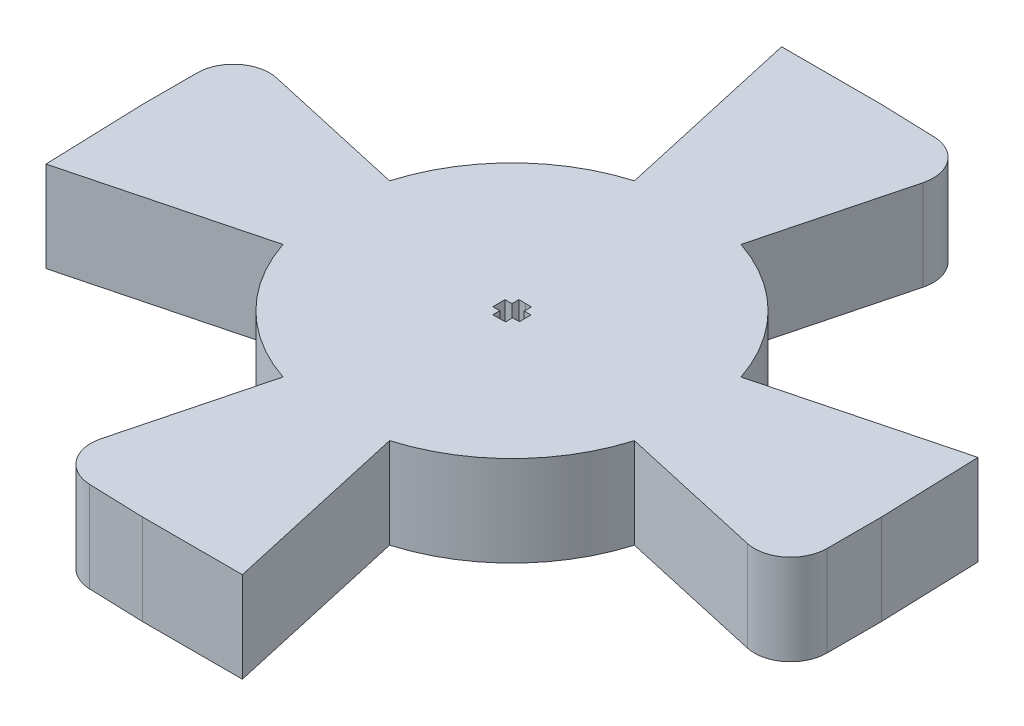
SolidWorks part; units mm, degrees
ref_plane "Front Plane" through (0, 0, 0) normal (0, 0, 1) x (1, 0, 0)
ref_plane "Top Plane" through (0, 0, 0) normal (0, 1, 0) x (1, 0, 0)
ref_plane "Right Plane" through (0, 0, 0) normal (1, 0, 0) x (0, 0, -1)
sketch "Sketch1" plane through (0, 0, 0) normal (0, 1, 0) x (1, 0, 0)
  line L0 (0.9504, 56.4023) -> (-0.9504, -56.4023) construction
  line L1 (-102.886, 0) -> (102.886, 0) construction
  line L2 (2.8313, -9.5908) -> (5.1777, -20.0637)
  line L3 (5.1777, -20.0637) -> (-0.3381, -20.0637)
  line L4 (-24.7302, 24.7302) -> (24.7302, -24.7302) construction
  line L5 (-31.3406, -31.3406) -> (31.3406, 31.3406) construction
  line L6 (-5.8507, -19.8779) -> (-0.3381, -20.0637)
  line L7 (-3.1528, -9.49) -> (-5.8507, -19.8779)
  line L8 (9.5908, -2.8313) -> (20.0637, -5.1777)
  line L9 (20.0637, -5.1777) -> (20.0637, 0.3381)
  line L10 (19.8779, 5.8507) -> (20.0637, 0.3381)
  line L11 (9.49, 3.1528) -> (19.8779, 5.8507)
  line L12 (-9.49, -3.1528) -> (-19.8779, -5.8507)
  line L13 (-19.8779, -5.8507) -> (-20.0637, -0.3381)
  line L14 (-20.0637, 5.1777) -> (-20.0637, -0.3381)
  line L15 (-9.5908, 2.8313) -> (-20.0637, 5.1777)
  line L16 (-2.8313, 9.5908) -> (-5.1777, 20.0637)
  line L17 (-5.1777, 20.0637) -> (0.3381, 20.0637)
  line L18 (5.8507, 19.8779) -> (0.3381, 20.0637)
  line L19 (3.1528, 9.49) -> (5.8507, 19.8779)
  line L20 (-0.3381, -0.7219) -> (-0.3381, 0.7219)
  line L21 (-0.3381, 0.7219) -> (0.0122, 0.7219)
  line L22 (0, 0.3381) -> (-0.7219, 0.3381)
  line L23 (-0.7219, 0.3381) -> (-0.7219, -0.0122)
  line L24 (0.7329, 0.3136) -> (0.7211, -0.0365)
  line L25 (0.0114, 0.3379) -> (0.7329, 0.3136)
  line L26 (0.3379, -0.0114) -> (0.3622, 0.7101)
  line L27 (0.3622, 0.7101) -> (0.0122, 0.7219)
  line L28 (-0.7219, -0.3381) -> (-0.7219, 0.0122)
  line L29 (0, -0.3381) -> (-0.7219, -0.3381)
  line L30 (-0.3381, -0.7219) -> (0.0122, -0.7219)
  line L31 (0.3622, -0.7101) -> (0.0122, -0.7219)
  line L32 (0.7329, -0.3136) -> (0.7211, 0.0365)
  line L33 (0.3379, 0.0114) -> (0.3622, -0.7101)
  line L34 (0.0114, -0.3379) -> (0.7329, -0.3136)
  circle A0 centre (0, 0) radius 10
  point P4 (0, 0)
  point P7 (0, 0)
  point P15 (0, 0)
  point P18 (0, 0)
  point P50 (-0.3381, 0)
extrude "Boss-Extrude1" add sketch "Sketch1" along normal blind 5 contours A0 L8 L9 L10 L11 | A0 | A0 L7 L6 L3 L2 | A0 L15 L14 L13 L12 | A0 L19 L18 L17 L16
fillet "Fillet1" radius 2 4 edges at (5.8507, 2.5, -19.8779) (20.0637, 2.5, 5.1777) (-5.8507, 2.5, 19.8779) (-20.0637, 2.5, -5.1777)
